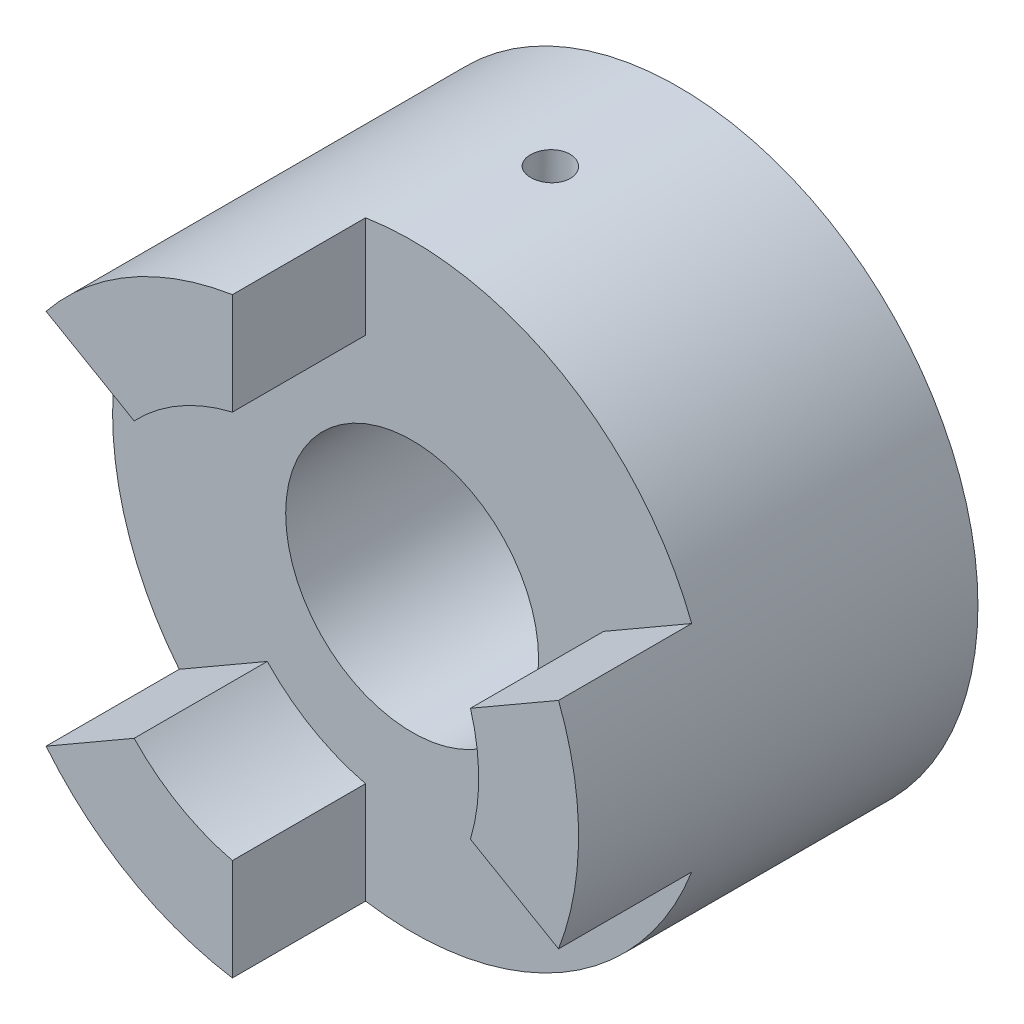
SolidWorks part; units mm, degrees
ref_plane "Front Plane" through (0, 0, 0) normal (0, 0, 1) x (1, 0, 0)
ref_plane "Top Plane" through (0, 0, 0) normal (0, 1, 0) x (1, 0, 0)
ref_plane "Right Plane" through (0, 0, 0) normal (1, 0, 0) x (0, 0, -1)
sketch "Sketch1" plane through (0, 0, 0) normal (0, 0, 1) x (1, 0, 0)
  circle A0 centre (0, 0) radius 22.5
  dimension "D1" = 45
extrude "Boss-Extrude1" add sketch "Sketch1" along normal blind 20
sketch "Sketch3" plane through (0, 0, 20) normal (0, 0, 1) x (1, 0, 0)
  circle A0 centre (0, 0) radius 9.5
  dimension "D1" = 19
extrude "Cut-Extrude1" cut sketch "Sketch3" against normal up to next
hole_wizard "Ø3.0mm Dowel Hole1" positions "3DSketch1" profile "Sketch4" hole size "Ø3.0" standard "ANSI Metric"
sketch3d "3DSketch1"
  point P0 (0.3326, 22.4975, 9.951)
sketch "Sketch4" plane through (0.3326, 22.4975, 9.951) normal (0, 0, 1) x (-0.9999, 0.0148, 0)
  line L0 (0, 0) -> (0, 22.9013)
  line L1 (0, 22.9013) -> (1.5, 22)
  line L2 (1.5, 22) -> (1.5, 0)
  line L5 (1.5, 0) -> (0, 0)
  line L10 (0, 22.9013) -> (-1.5, 22) construction
  line L11 (0, -6.35) -> (0, 107.95) construction
  dimension "Hole Dia." = 3
  dimension "Hole Depth" = 22
  dimension "Drill Angle" = 118
sketch "Sketch6" plane through (0, 0, 20) normal (0, 0, 1) x (1, 0, 0)
  line L0 (-3.5, 36.3116) -> (-3.5, -32.5042) construction
  line L1 (3.5, 36.3116) -> (3.5, -36.2663) construction
  line L2 (33.1967, -15.1247) -> (-26.3994, 19.2832) construction
  line L3 (29.6967, -21.1869) -> (-33.1575, 15.1021) construction
  line L4 (-29.6967, -21.1869) -> (29.8994, 13.221) construction
  line L5 (-33.1967, -15.1247) -> (29.6575, 21.1642) construction
  line L6 (-17.4984, 14.1441) -> (-10.8818, 10.3241)
  line L7 (-3.5, 22.2261) -> (-3.5, 14.586)
  line L8 (14.3818, 4.2619) -> (20.9984, 8.082)
  line L9 (20.9984, -8.082) -> (14.3818, -4.2619)
  line L10 (-3.5, -14.586) -> (-3.5, -22.2261)
  line L11 (-17.4984, -14.1441) -> (-10.8818, -10.3241)
  arc A0 (-3.5, 22.2261) -> (-17.4984, 14.1441) centre (0, 0) ccw
  arc A1 (-10.8818, -10.3241) -> (-3.5, -14.586) centre (0, 0) ccw
  arc A2 (-17.4984, -14.1441) -> (-3.5, -22.2261) centre (0, 0) ccw
  arc A3 (-3.5, 14.586) -> (-10.8818, 10.3241) centre (0, 0) ccw
  arc A4 (20.9984, -8.082) -> (20.9984, 8.082) centre (0, 0) ccw
  arc A5 (14.3818, -4.2619) -> (14.3818, 4.2619) centre (0, 0) ccw
  point P16 (0, 0)
  dimension "D3" = 30
  dimension "D4" = 45
  dimension "D1" = 7
  dimension "D2" = 3.5
extrude "Boss-Extrude3" add sketch "Sketch6" along normal blind 10
